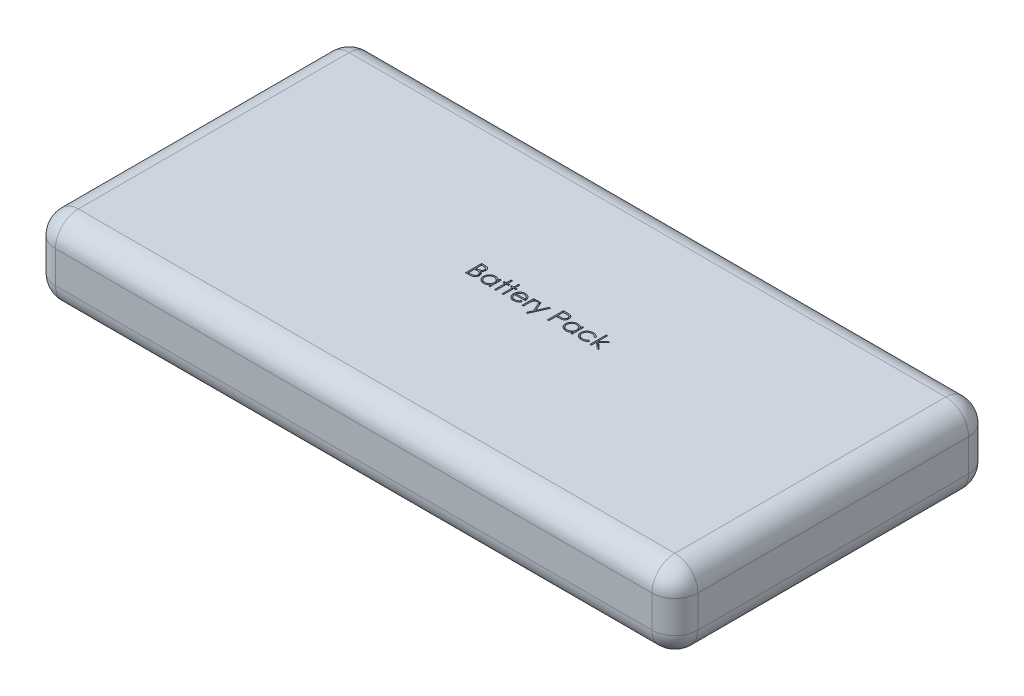
SolidWorks part; units mm, degrees
ref_plane "Front Plane" through (0, 0, 0) normal (0, 0, 1) x (1, 0, 0)
ref_plane "Top Plane" through (0, 0, 0) normal (0, 1, 0) x (1, 0, 0)
ref_plane "Right Plane" through (0, 0, 0) normal (1, 0, 0) x (0, 0, -1)
sketch "Sketch1" plane through (0, 0, 0) normal (0, 1, 0) x (1, 0, 0)
  line L1 (-70, -34.5) -> (70, -34.5)
  line L2 (-70, -34.5) -> (-70, 34.5)
  line L3 (-70, 34.5) -> (70, 34.5)
  line L4 (70, -34.5) -> (70, 34.5)
  line L5 (-70, -34.5) -> (70, 34.5) construction
  line L6 (-70, 34.5) -> (70, -34.5) construction
  point P0 (0, 0)
  dimension "D1" = 140
  dimension "D2" = 69
extrude "Boss-Extrude1" add sketch "Sketch1" along normal blind 17
fillet "Fillet1" radius 5 12 edges at (-70, 17, 0) (-70, 0, 0) (0, 17, -34.5) (-70, 8.5, -34.5) (0, 0, -34.5) (70, 17, 0) (70, 8.5, -34.5) (70, 0, 0) (-70, 8.5, 34.5) (0, 17, 34.5) (70, 8.5, 34.5) (0, 0, 34.5)
sketch "Sketch2" plane through (0, 17, 0) normal (0, 1, 0) x (1, 0, 0)
  text T0 "Battery Pack"
  point P1 (-11.2112, 0.651)
extrude "Cut-Extrude1" cut sketch "Sketch2" against normal blind 1
